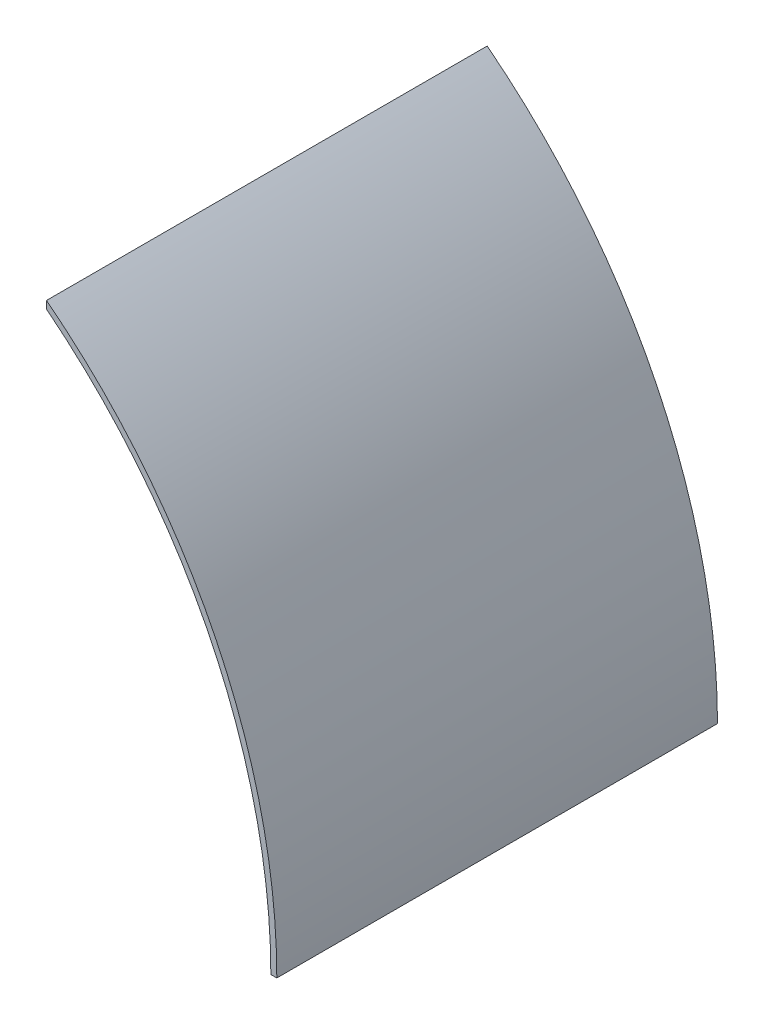
SolidWorks part; units mm, degrees
material "Plain Carbon Steel"
ref_plane "Front Plane" through (0, 0, 0) normal (0, 0, 1) x (1, 0, 0)
ref_plane "Top Plane" through (0, 0, 0) normal (0, 1, 0) x (1, 0, 0)
ref_plane "Right Plane" through (0, 0, 0) normal (1, 0, 0) x (0, 0, -1)
sketch "Sketch2" plane through (0, 0, 0) normal (0, 0, 1) x (1, 0, 0)
  line L0 (-150.8811, 0) -> (150.8811, 0) construction
  line L1 (0, 150.8811) -> (0, -152.4) construction
  line L2 (93.7311, 0) -> (93.7311, 108.9269) construction
  line L7 (93.7311, 120.1676) -> (93.7311, 118.2353)
  line L8 (0, -152.4) -> (0, -160.382) construction
  line L21 (150.8811, 0) -> (152.4, 0)
  circle A0 centre (0, 0) radius 150.8811 construction
  circle A1 centre (0, 0) radius 152.4 construction
  arc A2 (93.7311, 118.2353) -> (150.8811, 0) centre (0, 0) cw
  arc A3 (152.4, 0) -> (93.7311, 120.1676) centre (0, 0) ccw
  dimension "D1" = 301.7622
  dimension "D2" = 304.8
  dimension "D3" = 93.7311
extrude "Inner Ring - Right Side" add sketch "Sketch2" along normal blind 112.268
